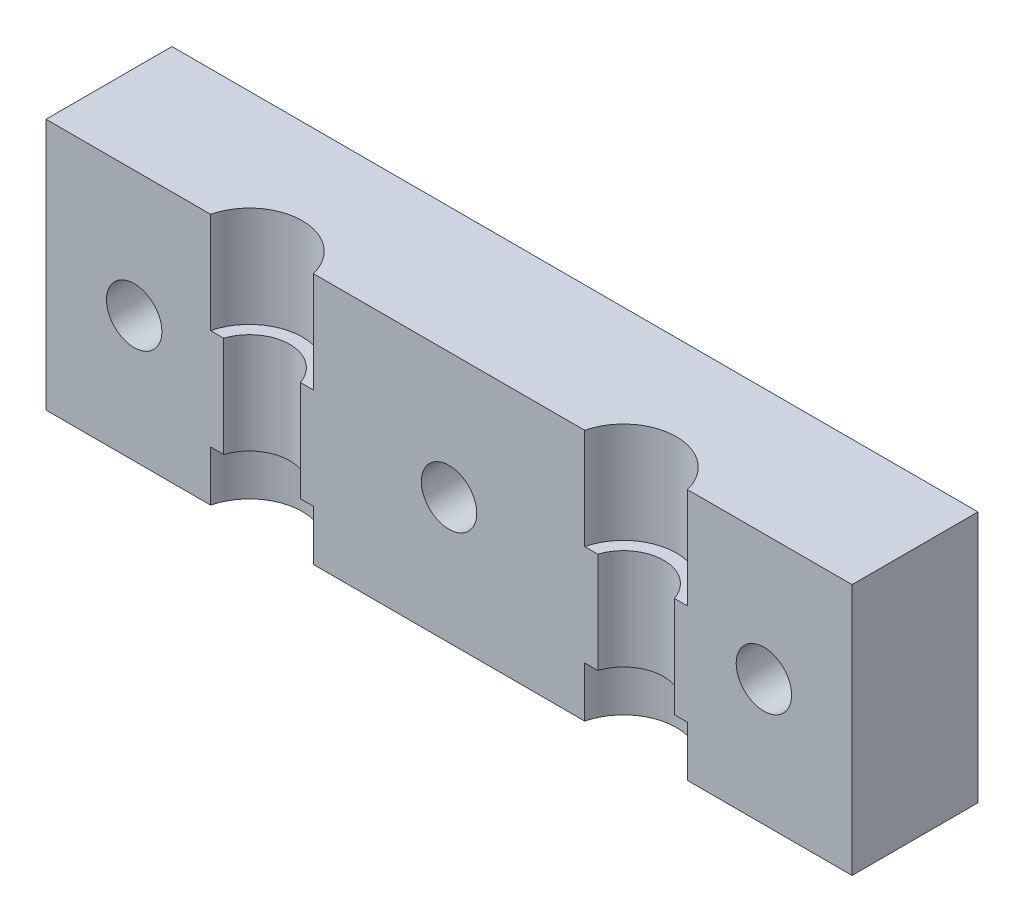
SolidWorks part; units mm, degrees
ref_plane "Спереди" through (0, 0, 0) normal (0, 0, 1) x (1, 0, 0)
ref_plane "Сверху" through (0, 0, 0) normal (0, 1, 0) x (1, 0, 0)
ref_plane "Справа" through (0, 0, 0) normal (1, 0, 0) x (0, 0, -1)
sketch "Эскиз1" plane through (0, 0, 0) normal (0, 0, 1) x (1, 0, 0)
  line L0 (0, 0) -> (0, 10)
  line L1 (0, 0) -> (32, 0)
  line L2 (0, 10) -> (32, 10)
  line L3 (32, 0) -> (32, 10)
  dimension "D1" = 10
  dimension "D2" = 32
extrude "Бобышка-Вытянуть1" add sketch "Эскиз1" along normal blind 5
sketch "Эскиз2" plane through (0, 10, 0) normal (0, 1, 0) x (1, 0, 0)
  line L0 (0, -5.5) -> (32, -5.5) construction
  line L1 (32, -5) -> (32, 0) construction
  line L2 (32, -5.5) -> (32, 0) construction
  line L3 (0, -5) -> (0, 0) construction
  line L4 (0, -5.5) -> (0, 0) construction
  line L5 (32, -5) -> (0, -5) construction
  line L6 (16, 0) -> (16, -5.5) construction
  line L7 (32, 0) -> (0, 0) construction
  circle A0 centre (8.575, -5.5) radius 2.1
  circle A1 centre (23.425, -5.5) radius 2.1
  circle A2 centre (16, -5.5) radius 7.425 construction
  dimension "D1" = 4.2
  dimension "D3" = 14.85
  dimension "D4" = 4.2
  dimension "D2" = 0.5
extrude "Вырез-Вытянуть1" cut sketch "Эскиз2" against normal through all
sketch "Эскиз3" plane through (0, 0, 5) normal (0, 0, 1) x (1, 0, 0)
  line L0 (0, 6) -> (32, 6) construction
  line L1 (0, 10) -> (0, 0) construction
  line L2 (32, 0) -> (32, 10) construction
  line L3 (6.5354, 10) -> (0, 10) construction
  dimension "D1" = 4
ref_plane "Плоскость1" through (0, 6, 0) normal (0, -1, 0) x (1, 0, 0)
sketch "Эскиз4" plane through (0, 6, 0) normal (0, -1, 0) x (1, 0, 0)
  line L0 (6.5354, 5) -> (7.0551, 5)
  line L1 (21.3854, 5) -> (21.9051, 5)
  line L2 (10.0949, 5) -> (10.6146, 5)
  line L3 (24.9449, 5) -> (25.4646, 5)
  arc A0 (6.5354, 5) -> (10.6146, 5) centre (8.575, 5.5) ccw construction
  arc A1 (21.3854, 5) -> (25.4646, 5) centre (23.425, 5.5) ccw construction
  arc A2 (6.5354, 5) -> (10.6146, 5) centre (8.575, 5.5) ccw
  arc A3 (21.3854, 5) -> (25.4646, 5) centre (23.425, 5.5) ccw
  arc A4 (7.0551, 5) -> (10.0949, 5) centre (8.575, 5.5) ccw
  arc A5 (21.9051, 5) -> (24.9449, 5) centre (23.425, 5.5) ccw
  dimension "D1" = 0.5
  dimension "D2" = 0.5
extrude "Бобышка-Вытянуть2" add sketch "Эскиз4" along normal blind 4
sketch "Эскиз5" plane through (0, 0, 0) normal (0, 0, -1) x (-1, 0, 0)
  circle A1 centre (-3.5, 5) radius 1.1
  circle A2 centre (-3.5, 5) radius 1.1
  circle A3 centre (-16, 5) radius 1.1
  circle A4 centre (-16, 5) radius 1.1
  circle A5 centre (-28.5, 5) radius 1.1
  circle A6 centre (-28.5, 5) radius 1.1
  dimension "D1" = 0
  dimension "D2" = 0
  dimension "D3" = 0
extrude "Вырез-Вытянуть2" cut sketch "Эскиз5" against normal through all
sketch "Эскиз6" plane through (0, 0, 0) normal (0, 0, -1) x (-1, 0, 0)
  line L0 (-28.5, 5) -> (-28.5, 7.4249) construction
  line L1 (-16, 2.5751) -> (-13.9, 3.7876)
  line L2 (-13.9, 3.7876) -> (-13.9, 6.2124)
  line L3 (-13.9, 6.2124) -> (-16, 7.4249)
  line L4 (-16, 7.4249) -> (-18.1, 6.2124)
  line L5 (-18.1, 6.2124) -> (-18.1, 3.7876)
  line L6 (-18.1, 3.7876) -> (-16, 2.5751)
  line L7 (-3.5, 2.5751) -> (-1.4, 3.7876)
  line L8 (-1.4, 3.7876) -> (-1.4, 6.2124)
  line L9 (-1.4, 6.2124) -> (-3.5, 7.4249)
  line L10 (-3.5, 7.4249) -> (-5.6, 6.2124)
  line L11 (-5.6, 6.2124) -> (-5.6, 3.7876)
  line L12 (-5.6, 3.7876) -> (-3.5, 2.5751)
  line L13 (-28.5, 2.5751) -> (-26.4, 3.7876)
  line L14 (-26.4, 3.7876) -> (-26.4, 6.2124)
  line L15 (-26.4, 6.2124) -> (-28.5, 7.4249)
  line L16 (-28.5, 7.4249) -> (-30.6, 6.2124)
  line L17 (-30.6, 6.2124) -> (-30.6, 3.7876)
  line L18 (-30.6, 3.7876) -> (-28.5, 2.5751)
  line L19 (-16, 5) -> (-16, 7.4249) construction
  line L20 (-3.5, 5) -> (-3.5, 7.4249) construction
  circle A0 centre (-16, 5) radius 2.1 construction
  circle A1 centre (-3.5, 5) radius 2.1 construction
  circle A2 centre (-28.5, 5) radius 2.1 construction
  dimension "D1" = 4.2
  dimension "D2" = 4.2
  dimension "D3" = 4.2
extrude "Вырез-Вытянуть3" cut sketch "Эскиз6" against normal blind 1.6
